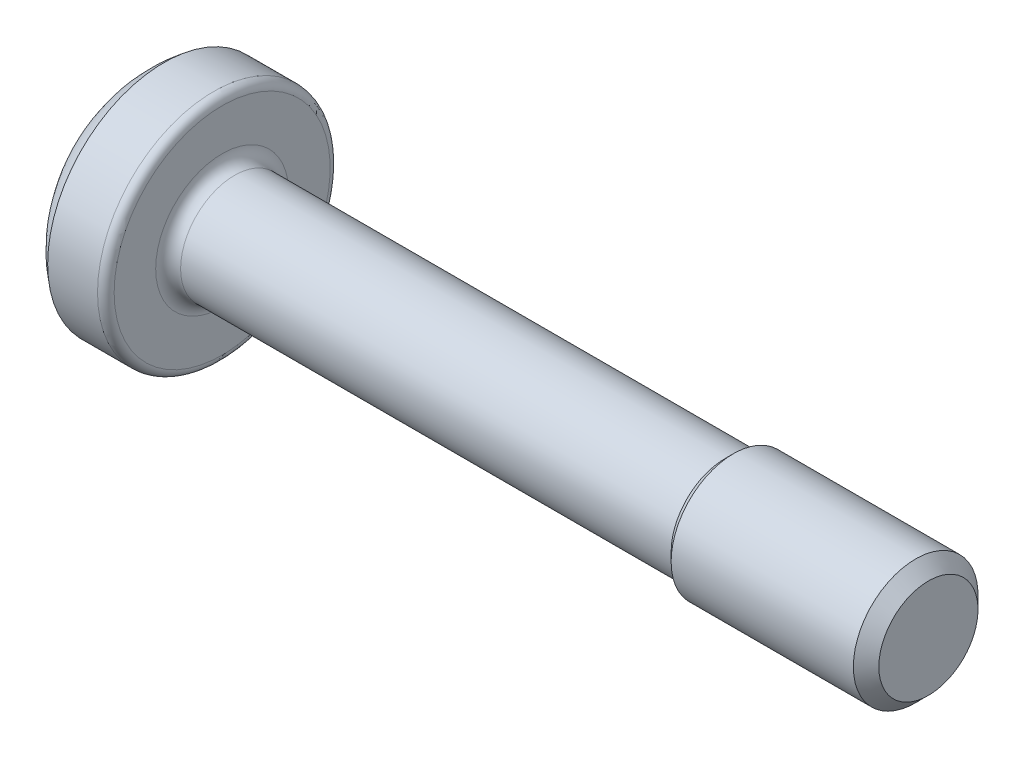
SolidWorks part; units mm, degrees
ref_plane "Front Plane" through (0, 0, 0) normal (0, 0, 1) x (1, 0, 0)
ref_plane "Top Plane" through (0, 0, 0) normal (0, 1, 0) x (1, 0, 0)
ref_plane "Right Plane" through (0, 0, 0) normal (1, 0, 0) x (0, 0, -1)
ref_plane "Plane1" through (0, 0, 0) normal (0, 0, 1) x (1, 0, 0)
sketch "Sketch1" plane through (0, 0, 0) normal (0, 0, 1) x (1, 0, 0)
  line L0 (-2.4, 0) -> (-2.4, 1.4)
  line L1 (-1.4, 2.8) -> (-0.2, 2.8)
  line L2 (0, 2.6) -> (0, 1.6)
  line L3 (0.3, 1.3) -> (12.1065, 1.3)
  line L4 (12.1065, 1.3) -> (12.3065, 1.5)
  line L5 (12.3065, 1.5) -> (16.6935, 1.5)
  line L6 (16.6935, 1.5) -> (17, 1.1935)
  line L7 (17, 1.1935) -> (17, 0)
  line L8 (17, 0) -> (-2.4, 0)
  line L9 (17, 0) -> (-2.4, 0) construction
  arc A0 (-2.4, 1.4) -> (-1.4, 2.8) centre (0.2683, 0.5512) cw
  arc A1 (-0.2, 2.8) -> (0, 2.6) centre (-0.2, 2.6) cw
  arc A2 (0, 1.6) -> (0.3, 1.3) centre (0.3, 1.6) ccw
revolve "Revolve1" add sketch "Sketch1" angle 360 about L9
cosmetic thread "Cosmetic Thread1" parameters "D1"=5, "D2"=2.387
ref_plane "Plane2" through (-2.4, 0, 0) normal (-1, 0, 0) x (0, 0, 1)
sketch "Sketch2" plane through (-2.4, 0, 0) normal (-1, 0, 0) x (0, 0, 1)
  line L0 (0.38, -2.0145) -> (0.38, -0.9755)
  line L1 (0.38, 0.9755) -> (0.38, 2.0145)
  line L2 (-0.38, 2.0145) -> (-0.38, 0.9755)
  line L3 (-0.38, -0.9755) -> (-0.38, -2.0145)
  arc A0 (-0.38, -2.0145) -> (0.38, -2.0145) centre (0, 0) ccw
  arc A1 (0.38, -0.9755) -> (0.8897, -0.8282) centre (0.7492, -1.2977) cw
  arc A2 (0.8897, -0.8282) -> (1.1621, -0.3564) centre (0.9699, -0.56) ccw
  arc A3 (1.1621, -0.3564) -> (1.1621, 0.3564) centre (1.4984, 0) cw
  arc A4 (1.1621, 0.3564) -> (0.8897, 0.8282) centre (0.9699, 0.56) ccw
  arc A5 (0.8897, 0.8282) -> (0.38, 0.9755) centre (0.7492, 1.2977) cw
  arc A6 (0.38, 2.0145) -> (-0.38, 2.0145) centre (0, 0) ccw
  arc A7 (-0.38, 0.9755) -> (-0.8897, 0.8282) centre (-0.7492, 1.2977) cw
  arc A8 (-0.8897, 0.8282) -> (-1.1621, 0.3564) centre (-0.9699, 0.56) ccw
  arc A9 (-1.1621, 0.3564) -> (-1.1621, -0.3564) centre (-1.4984, 0) cw
  arc A10 (-1.1621, -0.3564) -> (-0.8897, -0.8282) centre (-0.9699, -0.56) ccw
  arc A11 (-0.8897, -0.8282) -> (-0.38, -0.9755) centre (-0.7492, -1.2977) cw
extrude "Cut-Extrude1" cut sketch "Sketch2" against normal blind 2.1
ref_plane "Plane3" through (0, 0, 0) normal (0, 0, 1) x (1, 0, 0)
sketch "Sketch3" plane through (0, 0, 0) normal (0, 0, 1) x (1, 0, 0)
  line L0 (-2.4, 0) -> (-2.4, 1.4)
  line L1 (-2.4, 1.4) -> (-1, 0)
  line L2 (-1, 0) -> (-2.4, 0)
  line L3 (-1, 0) -> (-2.4, 0) construction
revolve "Cut-Revolve1" cut sketch "Sketch3" angle 360 about L3
